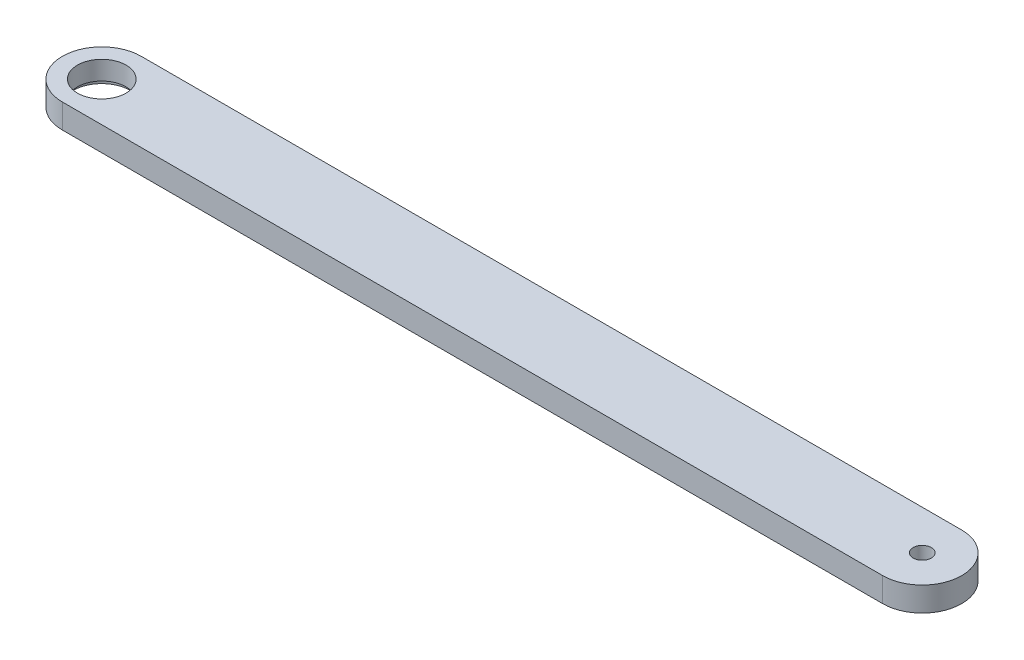
SolidWorks part; units mm, degrees
ref_plane "前视基准面" through (0, 0, 0) normal (0, 0, 1) x (1, 0, 0)
ref_plane "上视基准面" through (0, 0, 0) normal (0, 1, 0) x (1, 0, 0)
ref_plane "右视基准面" through (0, 0, 0) normal (1, 0, 0) x (0, 0, -1)
other "Configuration Table"
sketch "草图1" plane through (0, 0, 0) normal (0, 1, 0) x (1, 0, 0)
  line L0 (-67.5, 0) -> (67.5, 0) construction
  line L1 (-67.5, 6.5) -> (67.5, 6.5)
  line L2 (-67.5, -6.5) -> (67.5, -6.5)
  arc A0 (-67.5, 6.5) -> (-67.5, -6.5) centre (-67.5, 0) ccw
  arc A1 (67.5, -6.5) -> (67.5, 6.5) centre (67.5, 0) ccw
  point P3 (0, 0)
  dimension "D1" = 6.5
  dimension "D2" = 135
extrude "凸台-拉伸1" add sketch "草图1" along normal blind 4
sketch "草图3" plane through (0, 0, 0) normal (0, 1, 0) x (1, 0, 0)
  point P0 (-67.5, 0)
hole_wizard "M5 六角头螺栓的柱形沉头孔1" positions "草图3" profile "草图4" counterbore size "M5" standard "GB"
sketch "草图4" plane through (-67.5, 0, 0) normal (1, 0, 0) x (0, 0, -1)
  line L0 (0, 0) -> (0, 14.8034)
  line L1 (0, 14.8034) -> (4, 12.4)
  line L2 (4, 12.4) -> (4, 0.9)
  line L3 (4, 0.9) -> (4.75, 0.9)
  line L4 (4.75, 0.9) -> (4.75, 0)
  line L5 (4.75, 0) -> (0, 0)
  line L10 (0, 14.8034) -> (-4, 12.4) construction
  line L11 (0, -6.35) -> (0, 107.95) construction
  dimension "孔直径" = 8
  dimension "孔深度" = 12.4
  dimension "柱形沉头孔直径" = 9.5
  dimension "柱形沉头孔深度" = 0.9
  dimension "导头角度" = 118
sketch "草图5" plane through (0, 4, 0) normal (0, 1, 0) x (1, 0, 0)
  point P0 (67.5, 0)
hole_wizard "M3 螺纹孔1" positions "草图5" profile "草图6" tap size "M3" standard "GB"
sketch "草图6" plane through (67.5, 4, 0) normal (1, 0, 0) x (0, 0, 1)
  line L0 (0, 0) -> (0, 8.4013)
  line L1 (0, 8.4013) -> (1.5, 7.5)
  line L2 (1.5, 7.5) -> (1.5, 0)
  line L5 (1.5, 0) -> (0, 0)
  line L10 (0, 8.4013) -> (-1.5, 7.5) construction
  line L11 (0, -6.35) -> (0, 107.95) construction
  dimension "螺纹孔钻头直径" = 3
  dimension "螺纹孔钻头深度" = 7.5
  dimension "导头角度" = 118
cosmetic thread "孔螺蚊线1" parameters "D1"=6, "D2"=3
